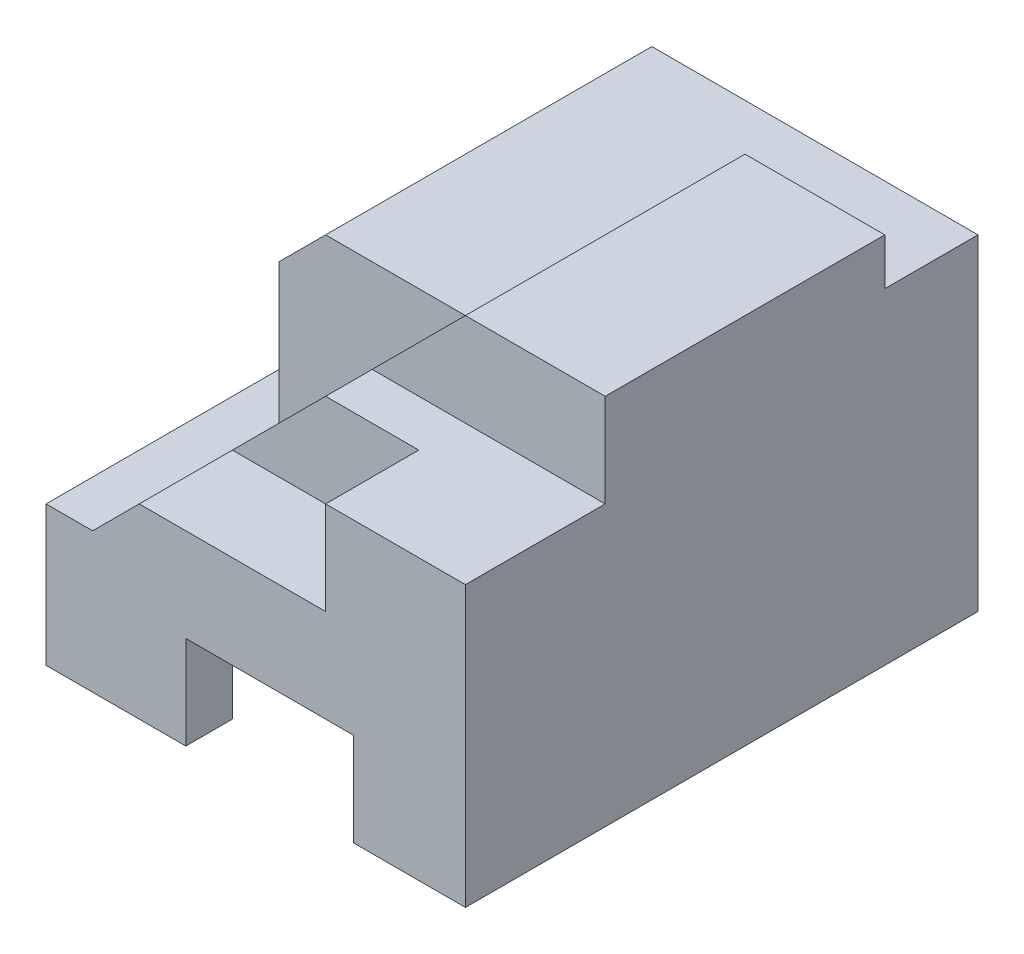
SolidWorks part; units mm, degrees
ref_plane "Front Plane" through (0, 0, 0) normal (0, 0, 1) x (1, 0, 0)
ref_plane "Top Plane" through (0, 0, 0) normal (0, 1, 0) x (1, 0, 0)
ref_plane "Right Plane" through (0, 0, 0) normal (1, 0, 0) x (0, 0, -1)
sketch "Sketch1" plane through (0, 0, 0) normal (0, 0, 1) x (1, 0, 0)
  line L1 (0, 0) -> (10, 0)
  line L2 (0, 0) -> (0, 8)
  line L3 (0, 8) -> (10, 8)
  line L4 (10, 0) -> (10, 8)
  dimension "D1" = 8
  dimension "D2" = 10
extrude "Boss-Extrude1" add sketch "Sketch1" along normal blind 11
sketch "Sketch2" plane through (0, 0, 0) normal (-1, 0, 0) x (0, 0, 1)
  line L1 (0, 8) -> (2, 8)
  line L2 (0, 8) -> (0, 7)
  line L3 (0, 7) -> (2, 7)
  line L4 (2, 8) -> (2, 7)
  line L5 (11, 8) -> (8, 8)
  line L6 (11, 8) -> (11, 6)
  line L7 (11, 6) -> (8, 6)
  line L8 (8, 8) -> (8, 6)
  dimension "D1" = 1
  dimension "D2" = 2
  dimension "D3" = 3
extrude "Cut-Extrude1" cut sketch "Sketch2" against normal blind 11
sketch "Sketch3" plane through (0, 0, 11) normal (0, 0, 1) x (1, 0, 0)
  line L0 (10, 6) -> (0, 6) construction
  line L1 (7, 6) -> (0, 6)
  line L2 (7, 6) -> (7, 4)
  line L3 (7, 4) -> (0, 4)
  line L4 (0, 6) -> (0, 4)
  line L5 (0, 6) -> (0, 0) construction
  line L6 (10, 0) -> (10, 6) construction
  line L8 (7, 6) -> (3, 6)
  line L9 (7, 6) -> (7, 4)
  line L10 (7, 4) -> (3, 4)
  line L11 (3, 6) -> (3, 4)
  line M2 (10, 6) -> (0, 6)
  dimension "D1" = 3
  dimension "D2" = 2
  dimension "D3" = 4
extrude "Cut-Extrude2" cut sketch "Sketch3" against normal blind 2 contours L11 L3 L2 M2
sketch "Sketch4" plane through (0, 0, 11) normal (0, 0, 1) x (1, 0, 0)
  line L0 (3, 4) -> (2, 3)
  line L1 (2, 3) -> (2, 8)
  line L2 (2, 8) -> (7, 8)
  line L3 (7, 8) -> (3, 4)
  line L4 (0, 6) -> (0, 0) construction
  dimension "D1" = 2
  dimension "D2" = 3
  dimension "D3" = 1
  dimension "D4" = 4
extrude "Cut-Extrude3" cut sketch "Sketch4" against normal blind 4
sketch "Sketch5" plane through (0, 0, 7) normal (0, 0, 1) x (1, 0, 0)
  line L0 (7, 8) -> (6, 7)
  line L1 (7, 8) -> (5, 6) construction
  line L2 (6, 7) -> (2, 7)
  line L3 (2, 8) -> (2, 3) construction
  line L4 (2, 7) -> (0, 7)
  line L5 (0, 8) -> (0, 6) construction
  line L6 (0, 7) -> (0, 8)
  line L7 (0, 8) -> (7, 8)
  line L8 (7, 8) -> (6, 7)
  line M1 (2, 3) -> (7, 8)
  line M2 (7, 8) -> (2, 8)
  line M3 (2, 8) -> (2, 3)
  dimension "D1" = 1
extrude "Cut-Extrude4" cut sketch "Sketch5" against normal blind 5 contours L2 M1 M2 M3 | L7 L6 L4 M3
sketch "Sketch6" plane through (0, 0, 11) normal (0, 0, 1) x (1, 0, 0)
  line L1 (2, 3) -> (0, 3)
  line L2 (2, 3) -> (2, 8)
  line L3 (2, 8) -> (0, 8)
  line L4 (0, 3) -> (0, 8)
extrude "Cut-Extrude5" cut sketch "Sketch6" against normal blind 9
sketch "Sketch7" plane through (0, 0, 7) normal (0, 0, 1) x (1, 0, 0)
  line L0 (3, 7) -> (0, 4)
  line L1 (6, 7) -> (2, 7) construction
  line L2 (0, 7) -> (0, 3) construction
  line L3 (0, 4) -> (0, 7)
  line L4 (0, 7) -> (3, 7)
  dimension "D1" = 3
  dimension "D2" = 3
extrude "Cut-Extrude6" cut sketch "Sketch7" against normal blind 7
sketch "Sketch9" plane through (0, 3, 0) normal (0, 1, 0) x (1, 0, 0)
  line L0 (0, -2) -> (1, -3)
  line L1 (1, -3) -> (1, -11)
  line L2 (0, -11) -> (2, -11) construction
  line L3 (1, -11) -> (0, -11)
  line L4 (0, -2) -> (0, -11) construction
  line L5 (0, -11) -> (0, -2)
  dimension "D1" = 1
  dimension "D2" = 1
  dimension "D3" = 1
extrude "Cut-Extrude7" cut sketch "Sketch9" against normal blind 7
sketch "Sketch10" plane through (0, 0, 0) normal (0, -1, 0) x (1, 0, 0)
  line L0 (1, 3) -> (2, 4)
  line L1 (2, 4) -> (7.5951, 4)
  line L2 (1, 11) -> (1, 3) construction
  line L3 (1, 4.2865) -> (1, 3)
  line L4 (1, 11) -> (10, 11) construction
  line L5 (4, 11) -> (7.5951, 11)
  line L6 (4, 11) -> (4, 10)
  line L7 (4, 10) -> (1, 10)
  line L8 (7.5951, 11) -> (7.5951, 9.3283)
  line L9 (1, 10) -> (1, 4.2865)
  line L10 (7.5951, 4) -> (7.5951, 9.3283)
  line L11 (1, 3) -> (0, 2) construction
  dimension "D1" = 1
  dimension "D2" = 1
  dimension "D3" = 3
  dimension "D4" = 1
  dimension "D5" = 180
extrude "Cut-Extrude8" cut sketch "Sketch10" against normal blind 2
